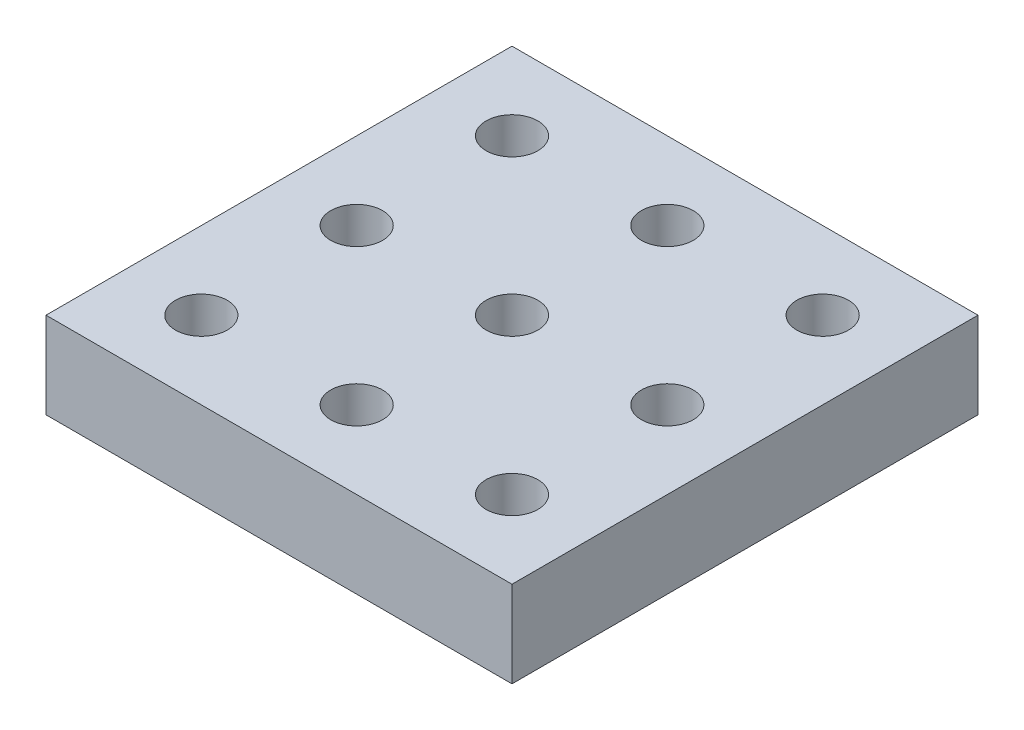
SolidWorks part; units mm, degrees
ref_plane "Front Plane" through (0, 0, 0) normal (0, 0, 1) x (1, 0, 0)
ref_plane "Top Plane" through (0, 0, 0) normal (0, 1, 0) x (1, 0, 0)
ref_plane "Right Plane" through (0, 0, 0) normal (1, 0, 0) x (0, 0, -1)
sketch "Sketch1" plane through (0, 0, 0) normal (0, 1, 0) x (1, 0, 0)
  line L1 (27, 27) -> (-27, 27)
  line L2 (27, 27) -> (27, -27)
  line L3 (27, -27) -> (-27, -27)
  line L4 (-27, 27) -> (-27, -27)
  line L5 (27, 27) -> (-27, -27) construction
  line L6 (27, -27) -> (-27, 27) construction
  circle A0 centre (0, 0) radius 3
  circle A1 centre (0, 0) radius 3
  circle A2 centre (-18, 0) radius 3
  circle A3 centre (-18, 18) radius 3
  circle A4 centre (0, 18) radius 3
  circle A5 centre (18, 18) radius 3
  circle A6 centre (18, 0) radius 3
  circle A7 centre (18, -18) radius 3
  circle A8 centre (0, -18) radius 3
  circle A9 centre (-18, -18) radius 3
  point P21 (0, 0)
extrude "Boss-Extrude1" add sketch "Sketch1" along normal blind 10 contours L1 L4 L3 L2 A9 A8 A7 A6 A5 A4 A3 A2 A0
